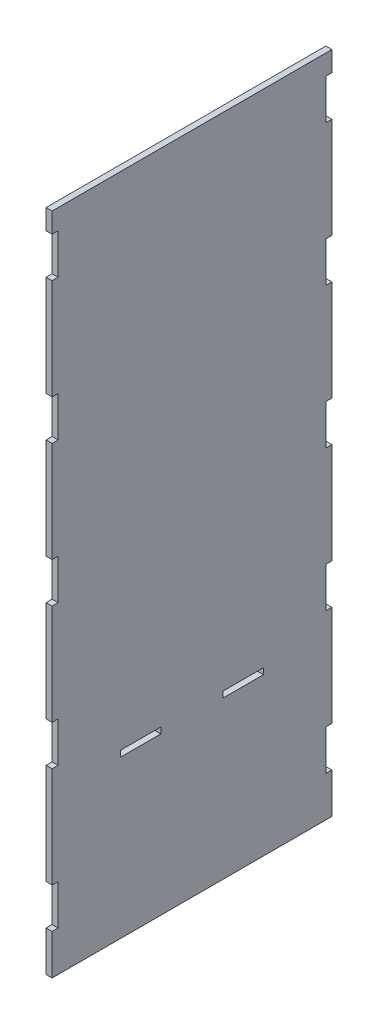
SolidWorks part; units mm, degrees
ref_plane "Спереди" through (0, 0, 0) normal (0, 0, 1) x (1, 0, 0)
ref_plane "Сверху" through (0, 0, 0) normal (0, 1, 0) x (1, 0, 0)
ref_plane "Справа" through (0, 0, 0) normal (1, 0, 0) x (0, 0, -1)
sketch "Эскиз1" plane through (0, 0, 0) normal (1, 0, 0) x (0, 0, -1)
  line L0 (-69.5, -165) -> (-69.5, -145)
  line L1 (-69.5, -165) -> (69.5, -165)
  line L2 (-69.5, -165) -> (-69.5, -145)
  line L3 (-69.5, 165) -> (69.5, 165)
  line L4 (69.5, -165) -> (69.5, -145)
  line L5 (-69.5, -165) -> (69.5, 165) construction
  line L6 (-69.5, 165) -> (69.5, -165) construction
  line L7 (-69.5, -145) -> (-66.5, -145)
  line L8 (-66.5, -145) -> (-66.5, -125)
  line L9 (-66.5, -125) -> (-69.5, -125)
  line L10 (-66.5, -75) -> (-66.5, -55)
  line L11 (-66.5, -55) -> (-69.5, -55)
  line L12 (-69.5, -75) -> (-66.5, -75)
  line L13 (-66.5, -5) -> (-66.5, 15)
  line L14 (-66.5, 15) -> (-69.5, 15)
  line L15 (-69.5, -5) -> (-66.5, -5)
  line L16 (-66.5, 65) -> (-66.5, 85)
  line L17 (-66.5, 85) -> (-69.5, 85)
  line L18 (-69.5, 65) -> (-66.5, 65)
  line L19 (-66.5, 135) -> (-66.5, 155)
  line L20 (-66.5, 155) -> (-69.5, 155)
  line L21 (-69.5, 135) -> (-66.5, 135)
  line L22 (0, 165) -> (0, 230.0878) construction
  line L23 (0, 230.0878) -> (0, -165) construction
  line L24 (66.5, 155) -> (69.5, 155)
  line L25 (66.5, 135) -> (66.5, 155)
  line L26 (69.5, 135) -> (66.5, 135)
  line L27 (66.5, 85) -> (69.5, 85)
  line L28 (66.5, 65) -> (66.5, 85)
  line L29 (69.5, 65) -> (66.5, 65)
  line L30 (66.5, 15) -> (69.5, 15)
  line L31 (66.5, -5) -> (66.5, 15)
  line L32 (69.5, -5) -> (66.5, -5)
  line L33 (66.5, -55) -> (69.5, -55)
  line L34 (66.5, -75) -> (66.5, -55)
  line L35 (69.5, -75) -> (66.5, -75)
  line L36 (69.5, -145) -> (66.5, -145)
  line L37 (66.5, -125) -> (69.5, -125)
  line L38 (66.5, -145) -> (66.5, -125)
  line L39 (-69.5, 155) -> (-69.5, 165)
  line L40 (69.5, 155) -> (69.5, 165)
  line L41 (69.5, 85) -> (69.5, 135)
  line L42 (-69.5, 85) -> (-69.5, 135)
  line L43 (69.5, 15) -> (69.5, 65)
  line L44 (-69.5, 15) -> (-69.5, 65)
  line L45 (-69.5, -55) -> (-69.5, -5)
  line L46 (69.5, -55) -> (69.5, -5)
  line L47 (69.5, -125) -> (69.5, -75)
  line L48 (-69.5, -125) -> (-69.5, -75)
  line L49 (-69.5, -165) -> (-69.5, -105.2)
  line L51 (69.5, -105) -> (69.5, -87)
  line L52 (35.5, -87) -> (15.5, -87)
  line L55 (-15.5, -87) -> (-35.5, -87)
  line L56 (-35.5, -87) -> (-35.5, -84)
  line L57 (-35.5, -84) -> (-15.5, -84)
  line L58 (-15.5, -84) -> (-15.5, -87)
  line L59 (35.5, -87) -> (35.5, -84)
  line L60 (35.5, -84) -> (15.5, -84)
  line L61 (15.5, -84) -> (15.5, -87)
  point P0 (0, 0)
  dimension "D1" = 330
  dimension "D2" = 139
  dimension "D3" = 5
  dimension "D4" = 20
  dimension "D5" = 20
  dimension "D6" = 3
  dimension "D7" = 19.8
  dimension "D8" = 18
  dimension "D9" = 34
  dimension "D10" = 34
  dimension "D11" = 20
extrude "Бобышка-Вытянуть5" add sketch "Эскиз1" along normal blind 3 contours L48 L9 L8 L7 L0 L1 L4 L36 L38 L37 L47 L35 L34 L33 L46 L32 L31 L30 L43 L29 L28 L27 L41 L26 L25 L24 L40 L3 L39 L20 L19 L21 L42 L17 L16 L18 L44 L14 L13 L15 L45 L11 L10 L12 L61 L60 L59
